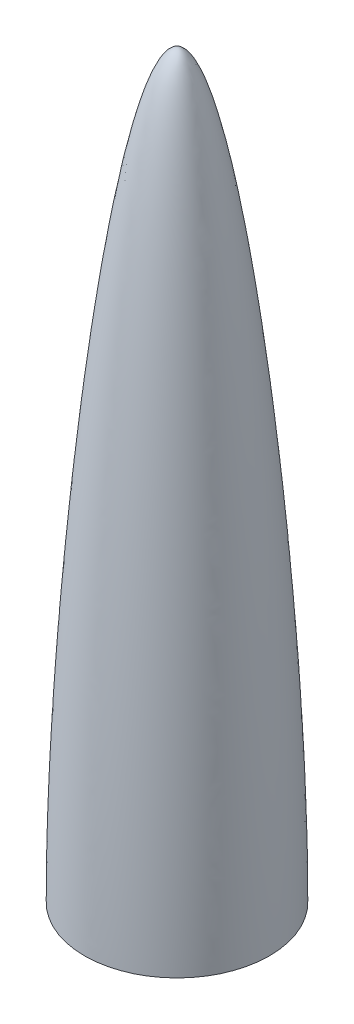
SolidWorks part; units mm, degrees
ref_plane "Front Plane" through (0, 0, 0) normal (0, 0, 1) x (1, 0, 0)
ref_plane "Top Plane" through (0, 0, 0) normal (0, 1, 0) x (1, 0, 0)
ref_plane "Right Plane" through (0, 0, 0) normal (1, 0, 0) x (0, 0, -1)
sketch "Sketch1" plane through (0, 0, 0) normal (0, 0, 1) x (1, 0, 0)
  line L2 (0, 403.0695) -> (0, 412.75)
  line L3 (0, 412.75) -> (25.4, 412.75) construction
  line L4 (25.4, 412.75) -> (51.5938, 152.4) construction
  line L5 (51.5938, 152.4) -> (51.5937, 0) construction
  line L6 (47.4599, 0) -> (51.5937, 0)
  line L9 (4.1275, 403.0695) -> (0, 403.0695)
  line L10 (0, 0) -> (0, 412.75) construction
  line L11 (4.1275, 4.1275) -> (4.1275, 403.0695) construction
  line L14 (47.4599, 4.1275) -> (47.4599, 0)
  line L15 (0, 0) -> (51.5937, 0) construction
  line L16 (4.1275, 4.1275) -> (47.4599, 4.1275) construction
  spline S0 degree 3 poles (0, 412.75) (25.4, 412.75) (51.5938, 152.4) (51.5937, 0) knots 0 0 0 0 1 1 1 1
  spline S1 degree 1 poles (4.1275, 403.0695) (47.4599, 4.1275) knots 0 0 1 1 construction
  spline S2 degree 3 poles (4.1275, 403.0695) (4.292, 402.7474) (4.6056, 402.1137) (5.259, 400.7143) (6.0805, 398.8028) (7.0801, 396.2359) (8.4208, 392.4721) (10.1053, 387.1472) (12.1235, 379.8324) (14.1288, 371.6512) (16.776, 359.6604) (20.0209, 342.7732) (23.7756, 319.872) (27.3599, 294.7243) (30.7442, 267.7155) (33.8997, 239.2284) (36.7981, 209.6445) (39.4112, 179.3444) (41.7111, 148.7085) (43.6699, 118.1168) (44.9949, 92.9775) (45.8566, 73.2684) (46.4002, 58.7355) (46.8378, 44.4989) (47.1112, 32.9225) (47.2735, 23.856) (47.3665, 17.164) (47.4305, 10.5671) (47.4534, 6.2836) (47.4599, 4.1275) knots 0.102456 0.102456 0.102456 0.102456 0.109398 0.11634 0.130223 0.144107 0.15799 0.185757 0.213524 0.241291 0.269058 0.324592 0.380127 0.435661 0.491195 0.546729 0.602263 0.657797 0.713331 0.768865 0.824399 0.852166 0.879933 0.9077 0.935467 0.949351 0.963234 0.977118 0.991002 0.991002 0.991002 0.991002
  dimension "D5" = 152.4
  dimension "D1" = 51.5937
  dimension "D2" = 4.1275
  dimension "D4" = 25.4
ref_axis "Central Axis" through (0, 433.3875, 0) along (0, -1, 0)
revolve "Revolve1" add sketch "Sketch1" angle 360 about axis through (0, 433.3875, 0) along (0, -1, 0)
